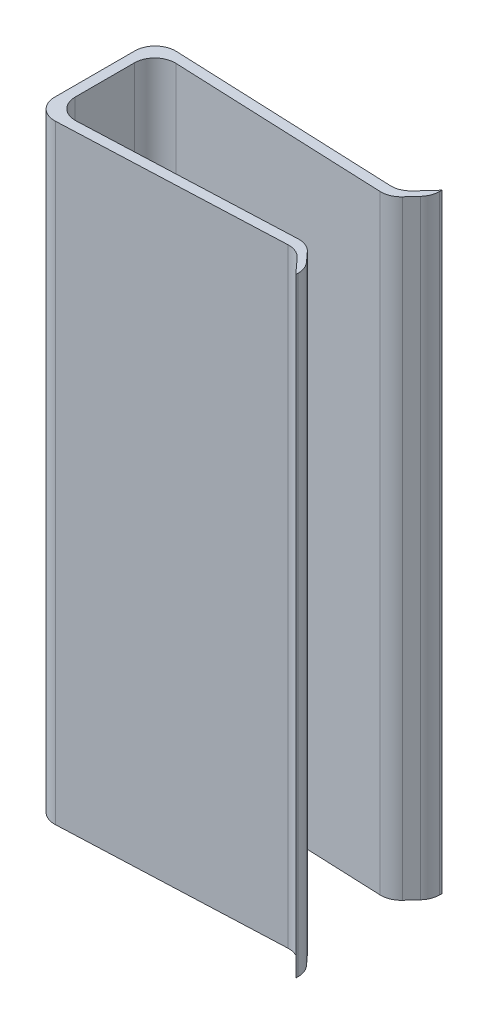
SolidWorks part; units mm, degrees
ref_plane "Front Plane" through (0, 0, 0) normal (0, 0, 1) x (1, 0, 0)
ref_plane "Top Plane" through (0, 0, 0) normal (0, 1, 0) x (1, 0, 0)
ref_plane "Right Plane" through (0, 0, 0) normal (1, 0, 0) x (0, 0, -1)
sketch "Sketch1" plane through (0, 0, 0) normal (0, 1, 0) x (1, 0, 0)
  line L0 (-6, -2.5) -> (-6, 2.5)
  line L1 (-6, 2.5) -> (6, 2.5) construction
  line L2 (-6, 2.5) -> (-6, -2.5) construction
  line L3 (-6, -2.5) -> (6, -2.5) construction
  line L4 (6, 2.5) -> (6, -2.5) construction
  line L5 (-6, 2.5) -> (6, -2.5) construction
  line L6 (-6, -2.5) -> (6, 2.5) construction
  line L7 (-6, 2.5) -> (6, 2)
  line L8 (6, 2) -> (7, 3.0957)
  line L9 (7, 3.0957) -> (7, 3.5957)
  line L10 (7, 3.5957) -> (6, 2.5)
  line L11 (6, 2.5) -> (-6.5, 3.0208)
  line L12 (-6.5, -3.0208) -> (-6.5, 3.0208)
  line L13 (0, 0) -> (6, 0) construction
  line L14 (7, -3.5957) -> (6, -2.5)
  line L15 (7, -3.0957) -> (7, -3.5957)
  line L16 (6, -2) -> (7, -3.0957)
  line L17 (-6, -2.5) -> (6, -2)
  line L18 (6, -2.5) -> (-6.5, -3.0208)
  point P0 (0, 0)
  point P10 (-6, 0)
  point P13 (-6.5, 0)
  dimension "D1" = 5
  dimension "D2" = 12
  dimension "D3" = 0.5
  dimension "D4" = 0.5
  dimension "D5" = 1
  dimension "D6" = 130
  dimension "D7" = 0.5
extrude "Boss-Extrude1" add sketch "Sketch1" along normal blind 30
fillet "Fillet1" radius 1 10 edges at (-6, 15, 2.5) (-6, 15, -2.5) (6, 15, 2) (7, 15, -3.0957) (7, 15, 3.0957) (6, 15, 2.5) (6, 15, -2.5) (6, 15, -2) (-6.5, 15, 3.0208) (-6.5, 15, -3.0208)
